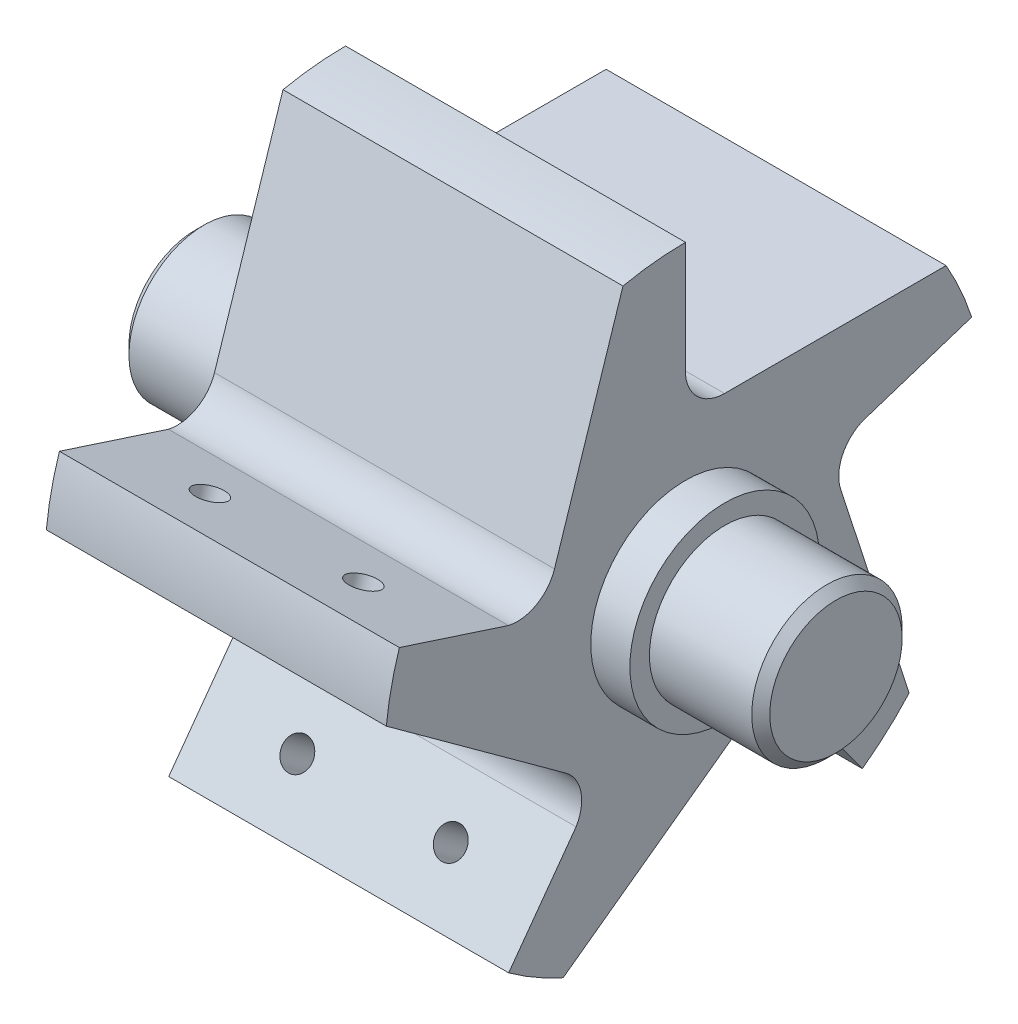
SolidWorks part; units mm, degrees
ref_plane "Front Plane" through (0, 0, 0) normal (0, 0, 1) x (1, 0, 0)
ref_plane "Top Plane" through (0, 0, 0) normal (0, 1, 0) x (1, 0, 0)
ref_plane "Right Plane" through (0, 0, 0) normal (1, 0, 0) x (0, 0, -1)
sketch "Sketch1" plane through (0, 0, 0) normal (1, 0, 0) x (0, 0, -1)
  line L0 (0, 25.4) -> (0, 15.7183)
  line L1 (3.2898, 12.7) -> (21.997, 12.7)
  line L2 (0, 0) -> (27.8951, 0) construction
  line L3 (24.1568, 7.849) -> (14.949, 4.8572)
  line L4 (13.095, 0.7957) -> (18.8759, -16.9959)
  line L5 (14.9297, -20.549) -> (9.239, -12.7164)
  line L6 (4.8034, -12.2082) -> (-10.3311, -23.2041)
  line L7 (-14.9297, -20.549) -> (-9.239, -12.7164)
  line L8 (-10.1264, -8.3408) -> (-25.2609, 2.655)
  line L9 (-24.1568, 7.849) -> (-14.949, 4.8572)
  line L10 (-11.0618, 7.0533) -> (-5.281, 24.8449)
  circle A0 centre (0, 0) radius 8.001 construction
  circle A1 centre (0, 0) radius 25.4
  arc A2 (0, 15.7183) -> (3.2898, 12.7) centre (3.2898, 16.002) ccw
  arc A3 (14.949, 4.8572) -> (13.095, 0.7957) centre (16.2354, 1.8161) ccw
  arc A4 (9.239, -12.7164) -> (4.8034, -12.2082) centre (6.7442, -14.8796) ccw
  arc A5 (-9.239, -12.7164) -> (-10.1264, -8.3408) centre (-12.0672, -11.0122) ccw
  arc A6 (-14.949, 4.8572) -> (-11.0618, 7.0533) centre (-14.2022, 8.0737) ccw
  point P32 (0, 0)
  dimension "D1" = 16.002
  dimension "D2" = 50.8
  dimension "D4" = 3.302
  dimension "D3" = 12.7
  dimension "D5" = 5
extrude "Boss-Extrude1" add sketch "Sketch1" along normal blind 28.702
sketch "Sketch9" plane through (28.702, 0, 0) normal (1, 0, 0) x (0, 0, -1)
  circle A0 centre (0, 0) radius 8.001
  circle A1 centre (0, 0) radius 6.35
  dimension "D1" = 16.002
  dimension "D2" = 12.7
extrude "Boss-Extrude2" add sketch "Sketch9" along normal blind 3.302
sketch "Sketch16" plane through (28.702, 0, 0) normal (1, 0, 0) x (0, 0, -1)
  circle A0 centre (0, 0) radius 6.35
  dimension "D1" = 12.7
extrude "Boss-Extrude3" add sketch "Sketch16" along normal blind 12.7
chamfer "Chamfer1" distance 0.762 angle 45 1 edges at (41.402, 0, -6.35)
ref_plane "Plane1" through (14.351, 0, 0) normal (1, 0, 0) x (0, 0, -1)
mirror "Mirror1" about plane through (14.351, 0, 0) normal (1, 0, 0) of "Boss-Extrude2", "Chamfer1", "Boss-Extrude3"
sketch "Sketch17" plane through (0, 0, 0) normal (0, 0, -1) x (-1, 0, 0)
  line L0 (-28.702, 25.4) -> (0, 25.4) construction
  line L1 (0, 26.7322) -> (0, -26.7322) construction
  line L2 (-14.351, 26.7322) -> (-14.351, -26.7322) construction
  circle A0 centre (-7.874, 20.32) radius 1.27
  circle A2 centre (-20.828, 20.32) radius 1.27
  dimension "D3" = 2.54
  dimension "D1" = 5.08
  dimension "D2" = 7.874
extrude "Cut-Extrude1" cut sketch "Sketch17" against normal blind 4.572 contours A2 | A0
pattern_circular "CirPattern1" count 5 over 360 about axis through (0, 0, 0) along (1, 0, 0) of "Cut-Extrude1"
